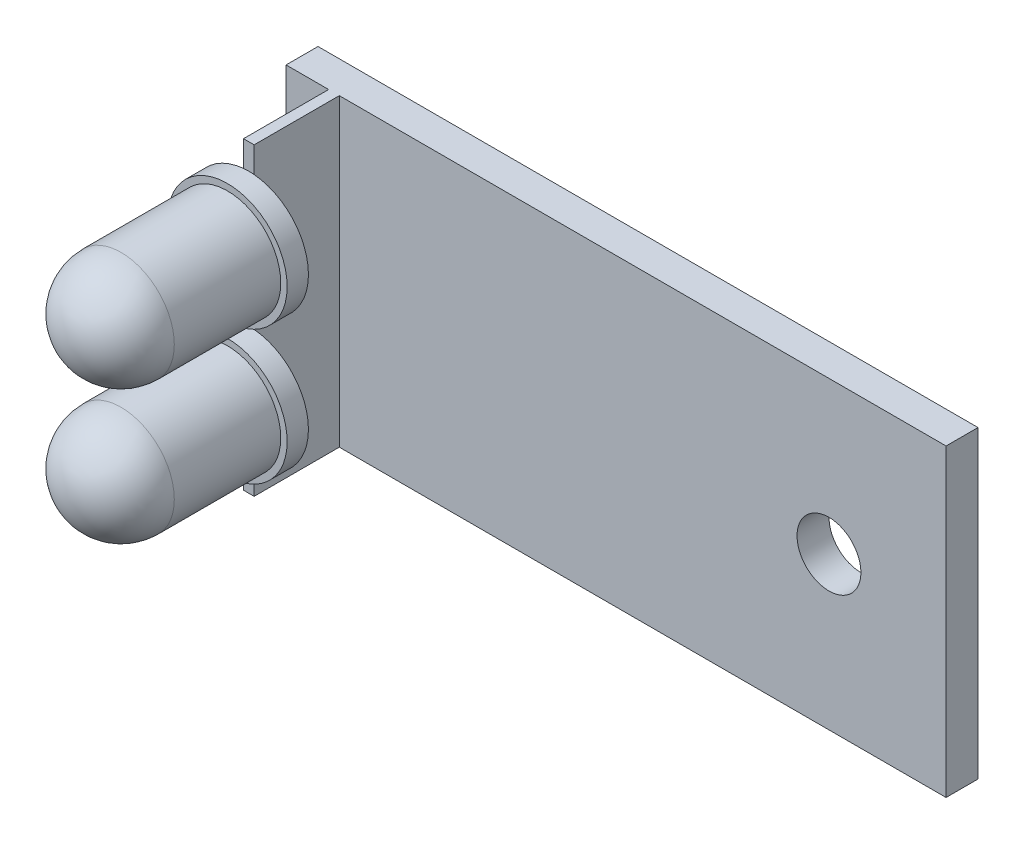
SolidWorks part; units mm, degrees
ref_plane "Front Plane" through (0, 0, 0) normal (0, 0, 1) x (1, 0, 0)
ref_plane "Top Plane" through (0, 0, 0) normal (0, 1, 0) x (1, 0, 0)
ref_plane "Right Plane" through (0, 0, 0) normal (1, 0, 0) x (0, 0, -1)
sketch "Sketch1" plane through (0, 0, 0) normal (0, 0, 1) x (1, 0, 0)
  line L1 (0, -7.15) -> (31, -7.15)
  line L2 (0, -7.15) -> (0, 7.15)
  line L3 (0, 7.15) -> (31, 7.15)
  line L4 (31, -7.15) -> (31, 7.15)
  point P6 (0, 0)
  dimension "D1" = 31
  dimension "D2" = 14.3
extrude "Boss-Extrude1" add sketch "Sketch1" along normal blind 1.5
sketch "Sketch2" plane through (0, -7.15, 0) normal (0, -1, 0) x (1, 0, 0)
  line L0 (2.5, 1.5) -> (2.5, 5.5)
  line L1 (0, 1.5) -> (31, 1.5) construction
  line L3 (2, 1.5) -> (2, 5.5)
  line L5 (2, 5.5) -> (2.5, 5.5)
  line L6 (2.5, 1.5) -> (2, 1.5)
  line L7 (0, 1.5) -> (0, 0) construction
  point P5 (0, 0)
  point P8 (0, 3.5)
  point P9 (0, 3)
  point P10 (0, 0)
  point P13 (0, 3.5)
  point P14 (2.3628, 3.5)
  point P15 (3.5286, 3.5)
  point P16 (2.5, 5)
  point P17 (0, 0)
  dimension "D1" = 0.5
  dimension "D2" = 2
  dimension "D3" = 4
extrude "Boss-Extrude2" add sketch "Sketch2" against normal through all
ref_plane "Plane1" through (0, -3.15, 0) normal (0, -1, 0) x (-1, 0, 0)
sketch "Sketch4" plane through (0, -3.15, 0) normal (0, -1, 0) x (1, 0, 0)
  line L4 (2.25, 14) -> (2.25, 5.5)
  line L7 (2.25, 5.5) -> (5.05, 5.5)
  line L8 (5.05, 5.5) -> (5.05, 6.5)
  line L9 (5.05, 6.5) -> (4.75, 6.5)
  line L10 (4.75, 6.5) -> (4.75, 11.5)
  line L12 (2.5, 5.5) -> (2, 5.5) construction
  arc A1 (4.75, 11.5) -> (2.25, 14) centre (2.25, 11.5) ccw
  point P2 (0, 0)
  point P3 (4.75, 11.5)
  dimension "D1" = 1
  dimension "D2" = 2.5
  dimension "D4" = 8.5
revolve "Revolve1" add sketch "Sketch4" angle 360 about L4
mirror "Mirror1" about plane through (0, 0, 0) normal (0, 1, 0) of "Revolve1"
sketch "Sketch5" plane through (0, 0, 1.5) normal (0, 0, 1) x (1, 0, 0)
  line L0 (31, -7.15) -> (31, 7.15) construction
  circle A0 centre (25.5, 0) radius 1.5
  point P4 (31, 0)
  dimension "D1" = 3
  dimension "D2" = 5.5
extrude "Cut-Extrude1" cut sketch "Sketch5" against normal blind 1.5
